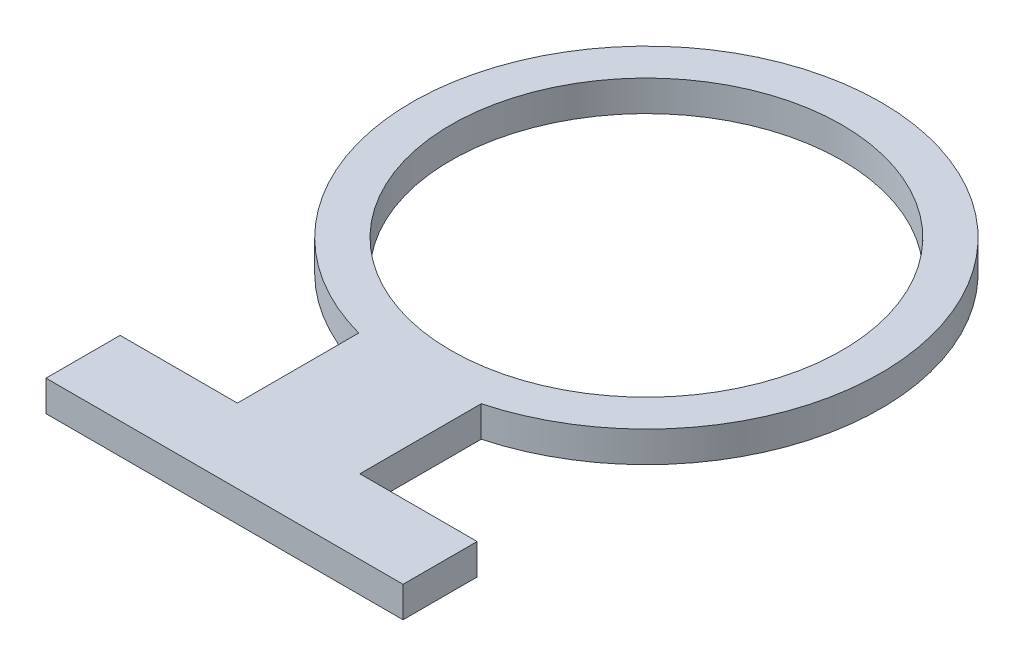
SolidWorks part; units mm, degrees
ref_plane "Front Plane" through (0, 0, 0) normal (0, 0, 1) x (1, 0, 0)
ref_plane "Top Plane" through (0, 0, 0) normal (0, 1, 0) x (1, 0, 0)
ref_plane "Right Plane" through (0, 0, 0) normal (1, 0, 0) x (0, 0, -1)
sketch "Sketch1" plane through (0, 0, 0) normal (0, 1, 0) x (1, 0, 0)
  line L0 (-19.8955, -73.5569) -> (19.8955, -73.5569)
  line L1 (19.8955, -73.5569) -> (19.8955, -112.9837)
  line L2 (57.9955, -112.9837) -> (57.9955, -137.0569)
  line L3 (57.9955, -137.0569) -> (-57.9955, -137.0569)
  line L4 (-57.9955, -137.0569) -> (-57.9955, -112.9837)
  line L5 (-57.9955, -112.9837) -> (-19.8955, -112.9837)
  line L6 (-19.8955, -112.9837) -> (-19.8955, -73.5569)
  line L7 (19.8955, -112.9837) -> (57.9955, -112.9837)
  circle A0 centre (0, 0) radius 63.5
  circle A1 centre (0, 0) radius 76.2
  dimension "D1" = 12.7
  dimension "D2" = 127
  dimension "D3" = 38.1
  dimension "D4" = 38.1
  dimension "D5" = 63.5
extrude "Boss-Extrude1" add sketch "Sketch1" along normal blind 10 contours L0 A1 A0 | A1 L6 L5 L4 L3 L2 L7 L1
